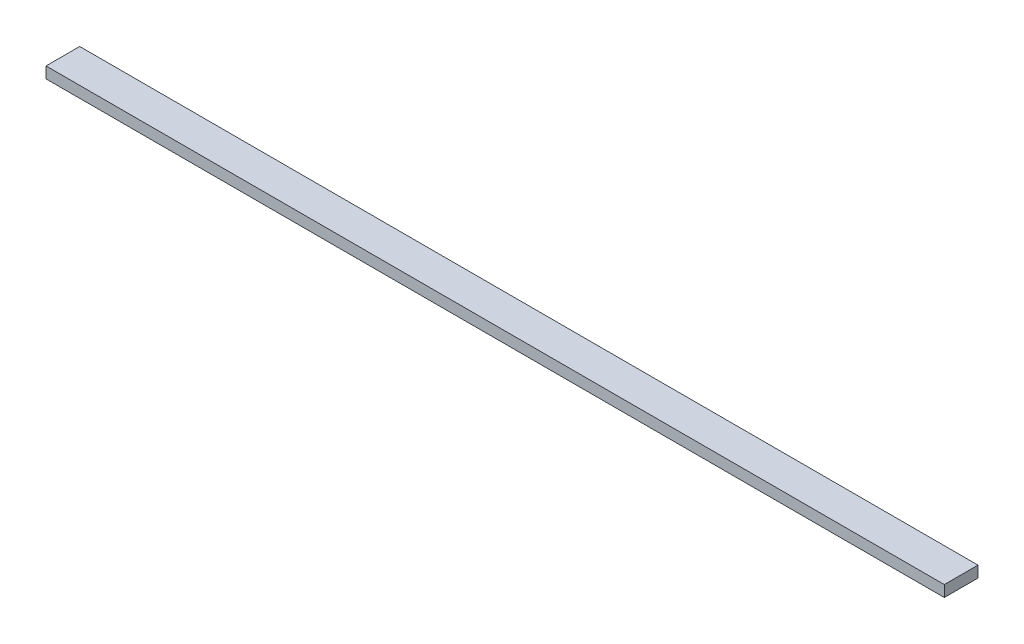
SolidWorks part; units mm, degrees
ref_plane "Front Plane" through (0, 0, 0) normal (0, 0, 1) x (1, 0, 0)
ref_plane "Top Plane" through (0, 0, 0) normal (0, 1, 0) x (1, 0, 0)
ref_plane "Right Plane" through (0, 0, 0) normal (1, 0, 0) x (0, 0, -1)
sketch "Sketch1" plane through (0, 0, 0) normal (0, 1, 0) x (1, 0, 0)
  line L0 (-400, 15) -> (400, -15) construction
  line L1 (-400, 15) -> (400, 15)
  line L2 (-400, 15) -> (-400, -15)
  line L3 (-400, -15) -> (400, -15)
  line L4 (400, 15) -> (400, -15)
  dimension "D1" = 800
  dimension "D2" = 30
extrude "Boss-Extrude1" add sketch "Sketch1" along normal blind 10
